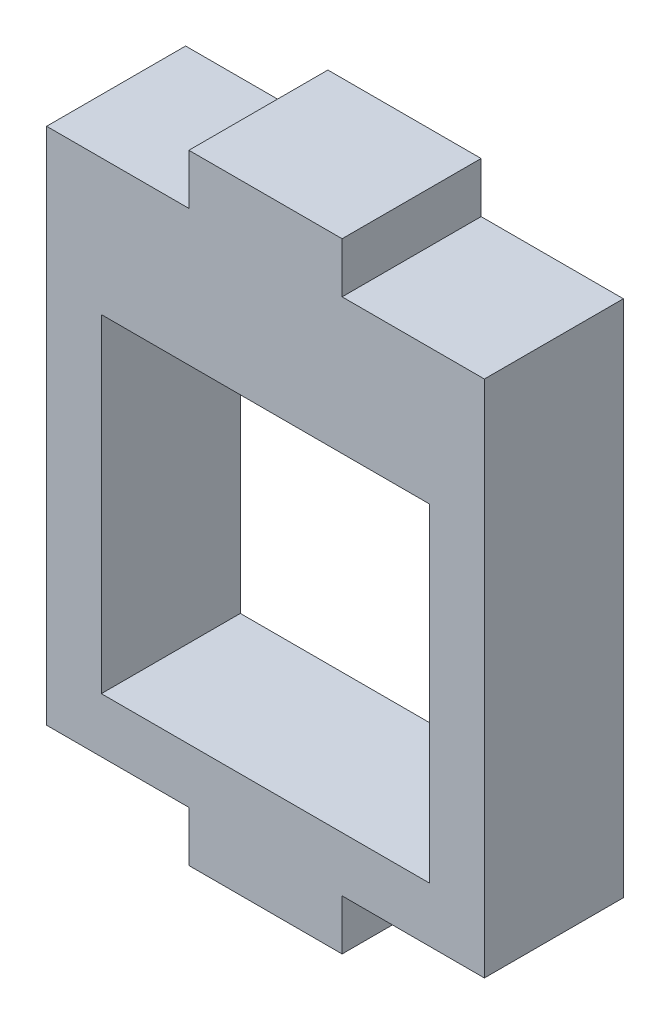
SolidWorks part; units mm, degrees
ref_plane "Front Plane" through (0, 0, 0) normal (0, 0, 1) x (1, 0, 0)
ref_plane "Top Plane" through (0, 0, 0) normal (0, 1, 0) x (1, 0, 0)
ref_plane "Right Plane" through (0, 0, 0) normal (1, 0, 0) x (0, 0, -1)
sketch "Sketch1" plane through (0, 0, 0) normal (0, 0, 1) x (1, 0, 0)
  line L0 (-15.2353, 17.8836) -> (-15.2353, 2.8836)
  line L1 (-15.2353, 2.8836) -> (-0.2353, 2.8836)
  line L2 (-0.2353, 2.8836) -> (-0.2353, 17.8836)
  line L3 (-0.2353, 17.8836) -> (2.2647, 17.8836)
  line L4 (2.2647, 17.8836) -> (2.2647, 0.3836)
  line L5 (2.2647, 0.3836) -> (-17.7353, 0.3836)
  line L6 (-17.7353, 0.3836) -> (-17.7353, 17.8836)
  line L7 (-17.7353, 17.8836) -> (-15.2353, 17.8836)
  dimension "D1" = 2.5
  dimension "D2" = 15
  dimension "D3" = 2.5
  dimension "D4" = 15
  dimension "D5" = 15
  dimension "D6" = 2.5
extrude "Boss-Extrude1" add sketch "Sketch1" along normal blind 6.35
sketch "Sketch2" plane through (0, 0, 0) normal (0, 0, 1) x (1, 0, 0)
  line L5 (-17.7353, 17.8836) -> (2.2647, 17.8836)
  line L6 (-17.7353, 17.8836) -> (-17.7353, 20.3836)
  line L7 (-17.7353, 20.3836) -> (2.2647, 20.3836)
  line L8 (2.2647, 17.8836) -> (2.2647, 20.3836)
  dimension "D1" = 20
  dimension "D2" = 2.5
extrude "Boss-Extrude2" add sketch "Sketch2" along normal through all
sketch "Sketch4" plane through (0, 0, 6.35) normal (0, 0, 1) x (1, 0, 0)
  line L0 (-17.7353, 0.3836) -> (2.2647, 0.3836) construction
  line L1 (-17.7353, 20.3836) -> (2.2647, 20.3836)
  line L2 (-17.7353, 20.3836) -> (-17.7353, 24.0836)
  line L3 (-17.7353, 24.0836) -> (-11.2353, 24.0836)
  line L4 (2.2647, 20.3836) -> (2.2647, 24.0836)
  line L6 (-11.2353, 24.0836) -> (-11.2353, 26.3836)
  line L7 (-11.2353, 26.3836) -> (-4.2353, 26.3836)
  line L8 (-4.2353, 24.0836) -> (-4.2353, 26.3836)
  line L9 (-11.2353, 0.3836) -> (-4.2353, 0.3836)
  line L10 (-11.2353, 0.3836) -> (-11.2353, -1.9164)
  line L11 (-11.2353, -1.9164) -> (-4.2353, -1.9164)
  line L12 (-4.2353, 0.3836) -> (-4.2353, -1.9164)
  line L13 (-17.7353, 20.3836) -> (-17.7353, 0.3836) construction
  line L14 (2.2647, 0.3836) -> (2.2647, 20.3836) construction
  line L15 (-4.2353, 24.0836) -> (2.2647, 24.0836)
  dimension "D1" = 3.7
  dimension "D2" = 20
  dimension "D3" = 7
  dimension "D4" = 2.3
  dimension "D5" = 6.5
  dimension "D6" = 6.5
  dimension "D7" = 7
  dimension "D8" = 2.3
  dimension "D9" = 6.5
extrude "Boss-Extrude3" add sketch "Sketch4" against normal blind 6.35
